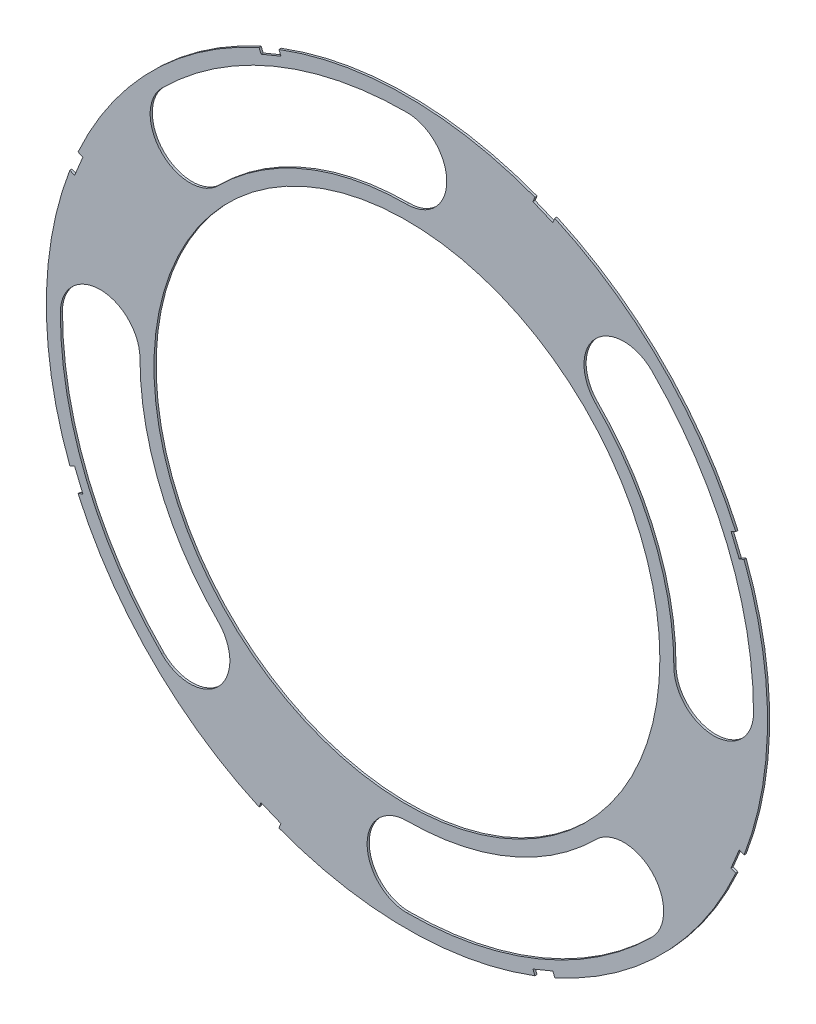
SolidWorks part; units mm, degrees
material "PTFE (general)"
ref_plane "Front Plane" through (0, 0, 0) normal (0, 0, 1) x (1, 0, 0)
ref_plane "Top Plane" through (0, 0, 0) normal (0, 1, 0) x (1, 0, 0)
ref_plane "Right Plane" through (0, 0, 0) normal (1, 0, 0) x (0, 0, -1)
sketch "Sketch4" plane through (0, 0, 0) normal (0, 0, 1) x (1, 0, 0)
  circle A0 centre (0, 0) radius 42.545
  dimension "D1" = 85.09
extrude "Boss-Extrude2" add sketch "Sketch4" along normal blind 0.254
sketch "Sketch5" plane through (0, 0, 0.254) normal (0, 0, 1) x (1, 0, 0)
  circle A0 centre (0, 0) radius 29.845
  circle A1 centre (0, 0) radius 42.545 construction
  dimension "D1" = 12.7
extrude "Cut-Extrude5" cut sketch "Sketch5" against normal through all
sketch "Sketch6" plane through (0, 0, 0.254) normal (0, 0, 1) x (1, 0, 0)
  line L0 (0, 0) -> (36.195, 0) construction
  line L1 (0, 0) -> (30.0839, -30.0839) construction
  line L2 (0, 0) -> (0, -42.545) construction
  line L3 (0, 0) -> (0, -42.545) construction
  line L4 (0, 0) -> (30.0839, -30.0839) construction
  line L5 (0, 0) -> (-30.0839, -30.0839) construction
  line L6 (0, 0) -> (-30.0839, -30.0839) construction
  line L7 (0, 0) -> (-42.545, 0) construction
  line L8 (0, 0) -> (-42.545, 0) construction
  line L9 (0, 0) -> (-30.0839, 30.0839) construction
  line L10 (0, 0) -> (-30.0839, 30.0839) construction
  line L11 (0, 0) -> (0, 42.545) construction
  line L12 (0, 0) -> (0, 42.545) construction
  line L13 (0, 0) -> (22.271, -22.271) construction
  line L14 (0, 0) -> (-22.271, -22.271) construction
  line L15 (0, 0) -> (30.0839, 30.0839) construction
  line L16 (0, 0) -> (30.0839, 30.0839) construction
  line L17 (0, 0) -> (42.545, 0) construction
  line L18 (0, 0) -> (42.545, 0) construction
  arc A0 (28.9164, 28.9164) -> (22.271, 22.271) centre (25.5937, 25.5937) ccw
  circle A1 centre (0, 0) radius 42.545 construction
  arc A2 (28.9164, -28.9164) -> (22.271, -22.271) centre (25.5937, -25.5937) ccw
  arc A3 (22.271, -22.271) -> (0, -31.496) centre (0, 0) cw
  arc A4 (0, -31.496) -> (0, -40.894) centre (0, -36.195) ccw
  arc A5 (0, -40.894) -> (28.9164, -28.9164) centre (0, 0) ccw
  arc A6 (-28.9164, -28.9164) -> (-22.271, -22.271) centre (-25.5937, -25.5937) ccw
  arc A7 (-22.271, -22.271) -> (-31.496, 0) centre (0, 0) cw
  arc A8 (-40.894, 0) -> (-28.9164, -28.9164) centre (0, 0) ccw
  arc A9 (-31.496, 0) -> (-40.894, 0) centre (-36.195, 0) ccw
  arc A10 (-28.9164, 28.9164) -> (-22.271, 22.271) centre (-25.5937, 25.5937) ccw
  arc A11 (-22.271, 22.271) -> (0, 31.496) centre (0, 0) cw
  arc A12 (0, 40.894) -> (-28.9164, 28.9164) centre (0, 0) ccw
  arc A13 (0, 31.496) -> (0, 40.894) centre (0, 36.195) ccw
  arc A14 (22.271, 22.271) -> (31.496, 0) centre (0, 0) cw
  arc A15 (40.894, 0) -> (28.9164, 28.9164) centre (0, 0) ccw
  circle A16 centre (0, 0) radius 29.845 construction
  arc A17 (31.496, 0) -> (40.894, 0) centre (36.195, 0) ccw
  point P4 (25.5937, -25.5937)
  point P11 (0, -36.195)
  point P13 (-25.5937, -25.5937)
  point P22 (25.5937, 25.5937)
  point P27 (-36.195, 0)
  point P30 (0, 0)
  point P36 (-25.5937, 25.5937)
  point P41 (0, 36.195)
  point P55 (36.195, 0)
  dimension "D2" = 4
  dimension "D3" = 45
  dimension "D4" = 90
  dimension "D6" = 6.35
  dimension "D7" = 9.398
  dimension "D8" = 4.699
  dimension "D9" = 4.699
  dimension "D5" = 6.35
  dimension "D10" = 90
extrude "Cut-Extrude6" cut sketch "Sketch6" against normal through all
sketch "Sketch8" plane through (0, 0, 0.254) normal (0, 0, 1) x (1, 0, 0)
  line L2 (40.3791, 15.3509) -> (39.4071, 17.6976)
  line L3 (40.3791, 15.3509) -> (39.2058, 14.8649)
  line L4 (39.2058, 14.8649) -> (38.2338, 17.2116)
  line L5 (39.4071, 17.6976) -> (38.2338, 17.2116)
  line L6 (0, 0) -> (50.4438, 0) construction
  line L7 (-15.3509, 40.3791) -> (-17.6976, 39.4071)
  line L8 (-15.3509, 40.3791) -> (-14.8649, 39.2058)
  line L9 (-17.6976, 39.4071) -> (-17.2116, 38.2338)
  line L10 (-14.8649, 39.2058) -> (-17.2116, 38.2338)
  line L11 (-17.6976, 39.4071) -> (-14.8649, 39.2058) construction
  line L12 (-15.3509, 40.3791) -> (-17.2116, 38.2338) construction
  line L13 (-39.4071, 17.6976) -> (-40.3791, 15.3509)
  line L14 (-39.4071, 17.6976) -> (-38.2338, 17.2116)
  line L15 (-38.2338, 17.2116) -> (-39.2058, 14.8649)
  line L16 (-40.3791, 15.3509) -> (-39.2058, 14.8649)
  line L17 (-39.4071, 17.6976) -> (-39.2058, 14.8649) construction
  line L18 (-40.3791, 15.3509) -> (-38.2338, 17.2116) construction
  line L19 (-40.3791, -15.3509) -> (-39.4071, -17.6976)
  line L20 (-40.3791, -15.3509) -> (-39.2058, -14.8649)
  line L21 (-39.2058, -14.8649) -> (-38.2338, -17.2116)
  line L22 (-39.4071, -17.6976) -> (-38.2338, -17.2116)
  line L23 (-40.3791, -15.3509) -> (-38.2338, -17.2116) construction
  line L24 (-39.4071, -17.6976) -> (-39.2058, -14.8649) construction
  line L25 (-17.6976, -39.4071) -> (-15.3509, -40.3791)
  line L26 (-17.6976, -39.4071) -> (-17.2116, -38.2338)
  line L27 (-17.2116, -38.2338) -> (-14.8649, -39.2058)
  line L28 (-15.3509, -40.3791) -> (-14.8649, -39.2058)
  line L29 (-17.6976, -39.4071) -> (-14.8649, -39.2058) construction
  line L30 (-15.3509, -40.3791) -> (-17.2116, -38.2338) construction
  line L31 (15.3509, -40.3791) -> (17.6976, -39.4071)
  line L32 (15.3509, -40.3791) -> (14.8649, -39.2058)
  line L33 (14.8649, -39.2058) -> (17.2116, -38.2338)
  line L34 (17.6976, -39.4071) -> (17.2116, -38.2338)
  line L35 (15.3509, -40.3791) -> (17.2116, -38.2338) construction
  line L36 (17.6976, -39.4071) -> (14.8649, -39.2058) construction
  line L37 (39.4071, -17.6976) -> (40.3791, -15.3509)
  line L38 (39.4071, -17.6976) -> (38.2338, -17.2116)
  line L39 (38.2338, -17.2116) -> (39.2058, -14.8649)
  line L40 (40.3791, -15.3509) -> (39.2058, -14.8649)
  line L41 (39.4071, -17.6976) -> (39.2058, -14.8649) construction
  line L42 (40.3791, -15.3509) -> (38.2338, -17.2116) construction
  line L43 (40.3791, 15.3509) -> (38.2338, 17.2116) construction
  line L44 (39.4071, 17.6976) -> (39.2058, 14.8649) construction
  line L45 (17.6976, 39.4071) -> (15.3509, 40.3791)
  line L46 (17.6976, 39.4071) -> (17.2116, 38.2338)
  line L47 (17.2116, 38.2338) -> (14.8649, 39.2058)
  line L48 (15.3509, 40.3791) -> (14.8649, 39.2058)
  line L49 (17.6976, 39.4071) -> (14.8649, 39.2058) construction
  line L50 (15.3509, 40.3791) -> (17.2116, 38.2338) construction
  circle A0 centre (0, 0) radius 42.545 construction
  point P3 (-16.2813, 39.3065)
  point P11 (-39.3065, 16.2813)
  point P15 (39.3065, 16.2813)
  point P20 (-39.3065, -16.2813)
  point P25 (-16.2813, -39.3065)
  point P26 (0, 0)
  point P31 (16.2813, -39.3065)
  point P36 (39.3065, -16.2813)
  point P45 (16.2813, 39.3065)
  point P46 (0, 0)
  dimension "D5" = 1.27
  dimension "D6" = 2.54
  dimension "D7" = 1.27
  dimension "D9" = 0.635
  dimension "D10" = 112.5
  dimension "D14" = 0.635
  dimension "D21" = 22.5
  dimension "D11" = 8
extrude "Cut-Extrude11" cut sketch "Sketch8" against normal through all
